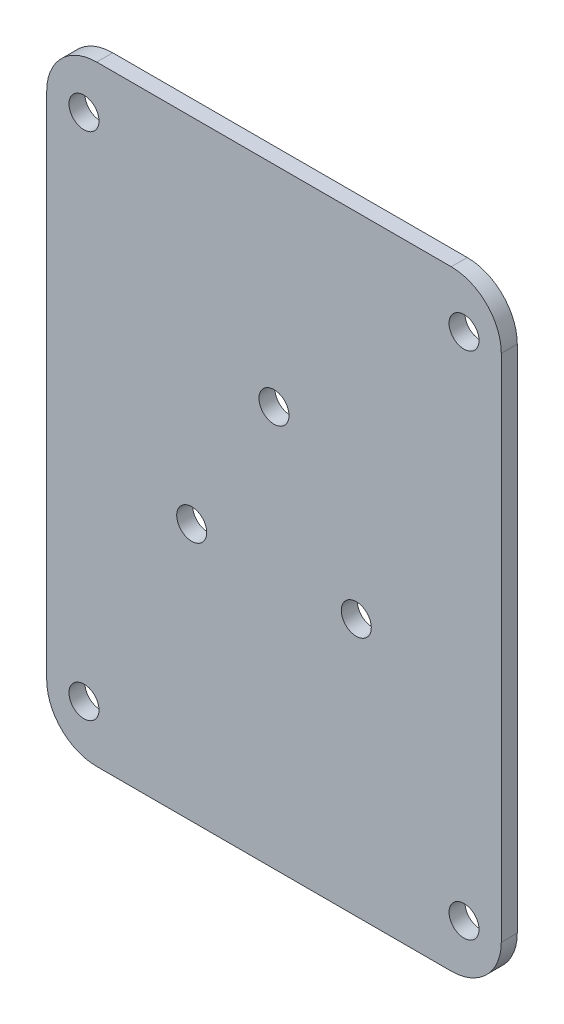
SolidWorks part; units mm, degrees
ref_plane "前视基准面" through (0, 0, 0) normal (0, 0, 1) x (1, 0, 0)
ref_plane "上视基准面" through (0, 0, 0) normal (0, 1, 0) x (1, 0, 0)
ref_plane "右视基准面" through (0, 0, 0) normal (1, 0, 0) x (0, 0, -1)
sketch "草图1" plane through (0, 0, 0) normal (0, 0, 1) x (1, 0, 0)
  line L0 (0, -18.2793) -> (0, 37.0285) construction
  line L1 (-19, 25.5) -> (19, 25.5) construction
  line L2 (-19, 25.5) -> (-19, -25.5) construction
  line L3 (-19, -25.5) -> (19, -25.5) construction
  line L4 (19, 25.5) -> (19, -25.5) construction
  line L5 (-19, 25.5) -> (19, -25.5) construction
  line L6 (-19, -25.5) -> (19, 25.5) construction
  line L7 (-22.7255, 30.5) -> (22.7255, 30.5)
  line L8 (-22.7255, 30.5) -> (-22.7255, -30.5)
  line L9 (-22.7255, -30.5) -> (22.7255, -30.5)
  line L10 (22.7255, 30.5) -> (22.7255, -30.5)
  line L11 (-22.7255, 30.5) -> (22.7255, -30.5) construction
  line L12 (-22.7255, -30.5) -> (22.7255, 30.5) construction
  line L13 (0, 0) -> (-8.3677, -4.8311) construction
  line L14 (0, 0) -> (8.3677, -4.8311) construction
  line L15 (0, 0) -> (21.7635, 0) construction
  line L16 (-9.5, -4.5) -> (9.5, -4.5) construction
  line L17 (0, 0) -> (-8.4161, 8.4161) construction
  line L18 (0, 0) -> (5.4814, 5.4814) construction
  circle A0 centre (19, -25.5) radius 1.5
  circle A1 centre (-19, -25.5) radius 1.5
  circle A2 centre (-19, 25.5) radius 1.5
  circle A3 centre (19, 25.5) radius 1.5
  circle A4 centre (0, 0) radius 9.5 construction
  circle A5 centre (-8.2272, -4.75) radius 1.5
  circle A6 centre (8.2272, -4.75) radius 1.5
  circle A7 centre (0, 9.5) radius 1.5
  point P0 (0, 0)
  point P10 (0, 0)
  dimension "D3" = 3
  dimension "D4" = 19
  dimension "D8" = 3
  dimension "D1" = 38
  dimension "D2" = 51
  dimension "D5" = 5
  dimension "D7" = 120
  dimension "D10" = 45
  dimension "D11" = 45
  dimension "D14" = 4.5
extrude "凸台-拉伸1" add sketch "草图1" along normal blind 1.6
fillet "圆角1" radius 5 4 edges at (-22.7255, 30.5, 0.8) (22.7255, 30.5, 0.8) (22.7255, -30.5, 0.8) (-22.7255, -30.5, 0.8)
